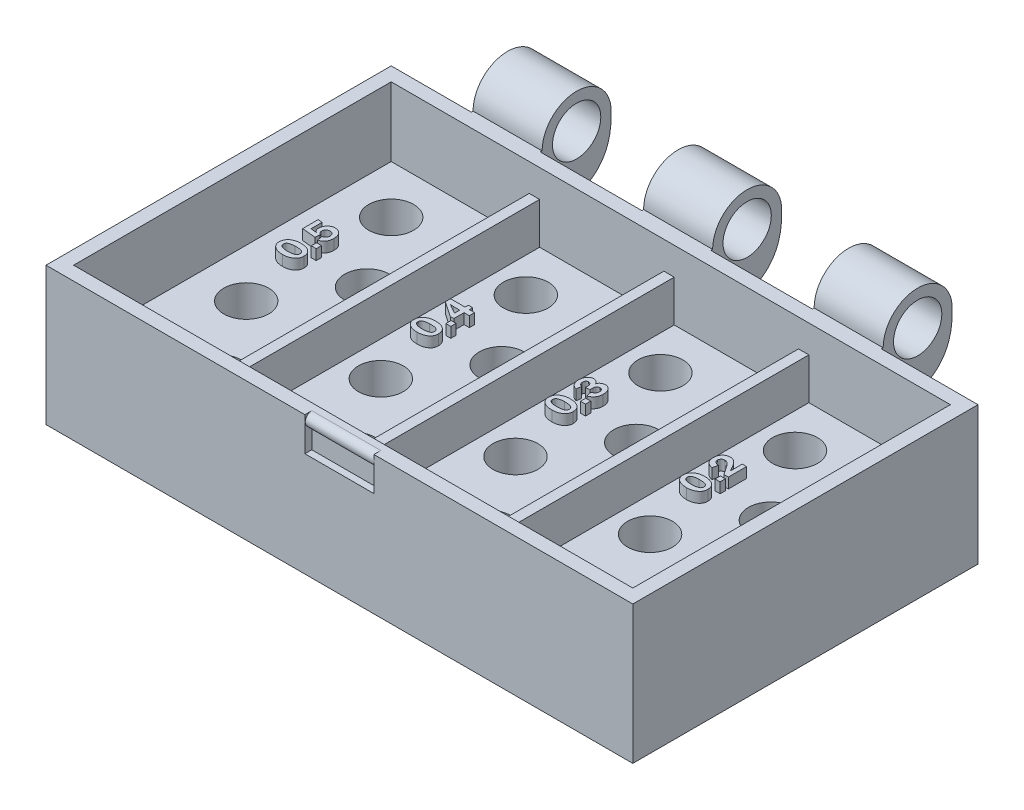
SolidWorks part; units mm, degrees
ref_plane "Plan de face" through (0, 0, 0) normal (0, 0, 1) x (1, 0, 0)
ref_plane "Plan de dessus" through (0, 0, 0) normal (0, 1, 0) x (1, 0, 0)
ref_plane "Plan de droite" through (0, 0, 0) normal (1, 0, 0) x (0, 0, -1)
sketch "Esquisse1" plane through (0, 0, 0) normal (0, 1, 0) x (1, 0, 0)
  line L1 (-42.5, 25) -> (42.5, 25)
  line L2 (-42.5, 25) -> (-42.5, -25)
  line L3 (-42.5, -25) -> (42.5, -25)
  line L4 (42.5, 25) -> (42.5, -25)
  line L5 (-42.5, 25) -> (42.5, -25) construction
  line L6 (-42.5, -25) -> (42.5, 25) construction
  point P0 (0, 0)
  dimension "D1" = 85
  dimension "D2" = 50
extrude "Boss.-Extru.1" add sketch "Esquisse1" along normal blind 20
shell "Coque1" thickness 2
sketch "Esquisse2" plane through (0, 10, 0) normal (0, 1, 0) x (1, 0, 0)
  line L0 (40.5, 23) -> (-40.5, 23) construction
  line L1 (-40.5, 23) -> (-40.5, -23) construction
  line L2 (-40.5, -23) -> (40.5, -23) construction
  line L3 (-40.5, 23) -> (-40.5, -23) construction
  circle A0 centre (-33.5, 16) radius 3.25
  circle A1 centre (-26.5, 5.5) radius 3.25
  circle A2 centre (-33.5, -5) radius 3.25
  circle A3 centre (-26.5, -16) radius 3.25
  dimension "D1" = 6.5
  dimension "D2" = 7
  dimension "D3" = 7
  dimension "D4" = 7
  dimension "D5" = 7
  dimension "D6" = 10.5
  dimension "D7" = 10.5
  dimension "D8" = 14
  dimension "D9" = 14
extrude "Enlèv. mat.-Extru.1" cut sketch "Esquisse2" against normal blind 6 contours A1 | A3 | A2 | A0
pattern_linear "Répétition linéaire1" count 4 spacing 19.5 along (1, 0, 0) of "Enlèv. mat.-Extru.1"
sketch "Esquisse3" plane through (0, 10, 0) normal (0, 1, 0) x (1, 0, 0)
  line L0 (40.5, 23) -> (-40.5, 23) construction
  line L1 (-20.5, 23) -> (-19, 23)
  line L2 (-20.5, 23) -> (-20.5, -23)
  line L3 (-20.5, -23) -> (-19, -23)
  line L4 (-19, 23) -> (-19, -23)
  line L5 (-40.5, -23) -> (40.5, -23) construction
  line L6 (-40.5, 23) -> (-40.5, -23) construction
  dimension "D1" = 1.5
  dimension "D2" = 20
extrude "Boss.-Extru.2" add sketch "Esquisse3" along normal blind 6 contours L2 L3 L4 L1
pattern_linear "Répétition linéaire2" count 3 spacing 19.5 along (1, 0, 0) of "Boss.-Extru.2"
sketch "Esquisse6" plane through (0, 10, 0) normal (0, 1, 0) x (1, 0, 0)
  text T0 "0.5" font "Franklin Gothic Medium" height 3.5
  text T1 "0.4" font "Franklin Gothic Medium" height 3.5
  text T2 "0.3" font "Franklin Gothic Medium" height 3.5
  text T3 "0.2" font "Franklin Gothic Medium" height 3.5
extrude "Boss.-Extru.4" add sketch "Esquisse6" along normal blind 1.5
ref_plane "Plan1" through (18.5, 0, 0) normal (1, 0, 0) x (0, 0, -1)
sketch "Esquisse7" plane through (18.5, 0, 0) normal (1, 0, 0) x (0, 0, -1)
  line L0 (-25, 20) -> (25, 20) construction
  line L1 (25, 20) -> (25, 0) construction
  line L2 (25.2612, 20) -> (25, 20)
  line L3 (25, 20) -> (25, 11.3828)
  circle A0 centre (30.2612, 20) radius 5
  spline S0 degree 2 poles (35.2612, 20) (35.6074, 10.8736) (25, 11.3828) knots 0 0 0 1 1 1
  dimension "D1" = 0
  dimension "D2" = 10
extrude "Boss.-Extru.5" add sketch "Esquisse7" along normal blind 10 contours A0 | S0 A0 L2 L3
sketch "Esquisse8" plane through (28.5, 0, 0) normal (1, 0, 0) x (0, 0, -1)
  circle A0 centre (30.2612, 20) radius 3.5
  arc A1 (35.2612, 20) -> (25.2612, 20) centre (30.2612, 20) ccw construction
  dimension "D1" = 7
  dimension "D2" = 0
extrude "Enlèv. mat.-Extru.2" cut sketch "Esquisse8" against normal up to surface (10 mm away) up to face at (18.5, 20.1729, -28.9132)
pattern_linear "Répétition linéaire4" count 3 spacing 24.7 along (1, 0, 0) of "Enlèv. mat.-Extru.2", "Boss.-Extru.5"
ref_plane "Plan2" through (0, 0, 0) normal (-1, 0, 0) x (0, 0, 1)
sketch "Esquisse9" plane through (0, 0, 0) normal (-1, 0, 0) x (0, 0, 1)
  line L1 (24, 18.0947) -> (24, 15.0947)
  line L2 (24, 15.0947) -> (25, 15.0947)
  line L3 (25, 20) -> (25, 0) construction
  line L4 (25, 15.0947) -> (25, 20)
  line L5 (25, 20) -> (24, 20)
  line L6 (-25, 20) -> (25, 20) construction
  arc A0 (24, 20) -> (24, 18.0947) centre (24, 19.0473) cw
  dimension "D5" = 3
  dimension "D1" = 1
  dimension "D2" = 1
  dimension "D3" = 0
  dimension "D4" = 1.9053
extrude "Enlèv. mat.-Extru.3" cut sketch "Esquisse9" against normal blind 5 and the other way blind 5
